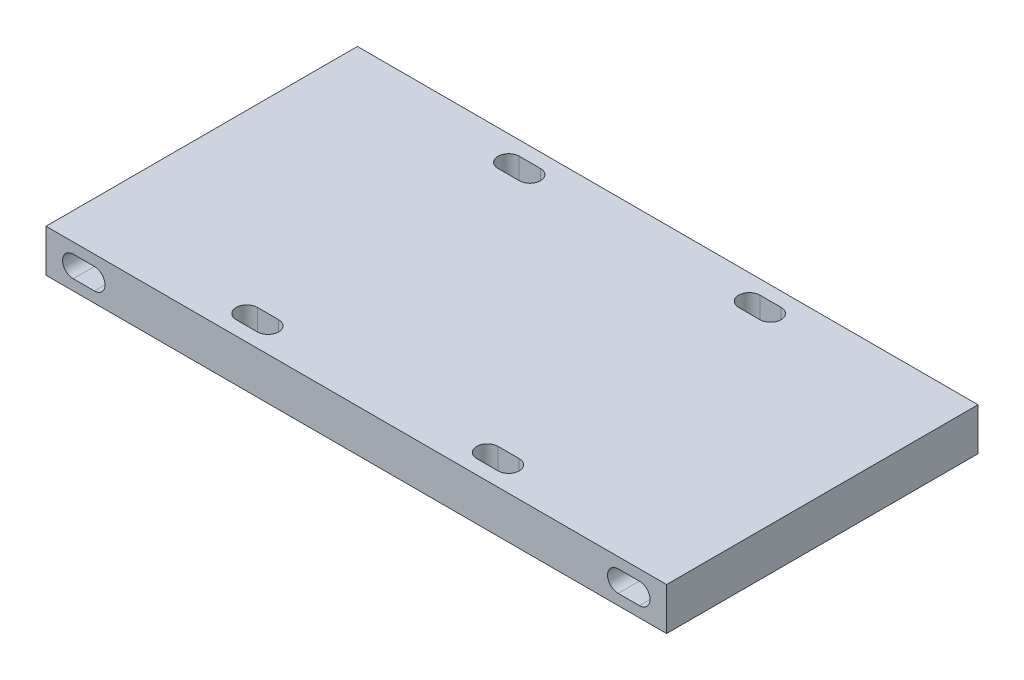
SolidWorks part; units mm, degrees
ref_plane "前视基准面" through (0, 0, 0) normal (0, 0, 1) x (1, 0, 0)
ref_plane "上视基准面" through (0, 0, 0) normal (0, 1, 0) x (1, 0, 0)
ref_plane "右视基准面" through (0, 0, 0) normal (1, 0, 0) x (0, 0, -1)
sketch "草图1" plane through (0, 0, 0) normal (0, 0, 1) x (1, 0, 0)
  line L0 (-40, 0) -> (40, 0) construction
  line L1 (-43.8406, 3) -> (43.8406, 3)
  line L2 (-43.8406, 3) -> (-43.8406, -3)
  line L3 (-43.8406, -3) -> (43.8406, -3)
  line L4 (43.8406, 3) -> (43.8406, -3)
  line L5 (-43.8406, 3) -> (43.8406, -3) construction
  line L6 (-43.8406, -3) -> (43.8406, 3) construction
  line L7 (-40, 0) -> (-37, 0) construction
  line L8 (-40, 1.5) -> (-37, 1.5)
  line L9 (-40, -1.5) -> (-37, -1.5)
  line L10 (0, 0) -> (0, 3) construction
  line L11 (40, 0) -> (37, 0) construction
  line L12 (40, 1.5) -> (37, 1.5)
  line L13 (40, -1.5) -> (37, -1.5)
  arc A0 (-40, 1.5) -> (-40, -1.5) centre (-40, 0) ccw
  arc A1 (-37, -1.5) -> (-37, 1.5) centre (-37, 0) ccw
  arc A2 (40, 1.5) -> (40, -1.5) centre (40, 0) cw
  arc A3 (37, -1.5) -> (37, 1.5) centre (37, 0) cw
  point P0 (0, 0)
  point P6 (-38.5, 0)
  point P9 (0, 0)
  point P18 (38.5, 0)
  dimension "D4" = 1.5
  dimension "D1" = 87.6812
  dimension "D2" = 6
  dimension "D3" = 3
extrude "凸台-拉伸1" add sketch "草图1" along normal blind 44
sketch "草图2" plane through (0, -3, 0) normal (0, -1, 0) x (-1, 0, 0)
  line L0 (2.1436, -22.9628) -> (9.3627, -10.4589)
  line L1 (9.3627, -10.4589) -> (4.6305, -10.4589)
  line L2 (4.6305, -10.4589) -> (-1.7817, -21.5652)
  line L3 (-1.7817, -21.5652) -> (0.0481, -26.5924)
  line L4 (0.0481, -26.5924) -> (-2.5682, -31.1239)
  line L5 (-2.5682, -31.1239) -> (-8.5375, -14.7234)
  line L6 (-8.5375, -14.7234) -> (-1.867, -14.7234)
  line L7 (-1.867, -14.7234) -> (-3.4191, -10.4589)
  line L8 (-3.4191, -10.4589) -> (-14.5058, -10.4589)
  line L9 (-14.5058, -10.4589) -> (-6.9844, -31.1239)
  point P9 (0, 0)
  dimension "D1" = 70
  dimension "D2" = 60
extrude "切除-拉伸-薄壁1" cut sketch "草图2" against normal blind 1 and the other way through all thin thin type mid plane wall 2
sketch "草图3" plane through (0, -3, 0) normal (0, -1, 0) x (1, 0, 0)
  line L0 (-18.9761, 40.5) -> (-15.9761, 40.5) construction
  line L1 (-18.9761, 40.5) -> (18.0239, 40.5)
  line L2 (-18.9761, 40.5) -> (-18.9761, 3.5)
  line L3 (-18.9761, 3.5) -> (18.0239, 3.5)
  line L4 (18.0239, 40.5) -> (18.0239, 3.5)
  line L5 (-18.9761, 40.5) -> (18.0239, 3.5) construction
  line L6 (-18.9761, 3.5) -> (18.0239, 40.5) construction
  line L7 (-18.9761, 42) -> (-15.9761, 42)
  line L8 (-18.9761, 39) -> (-15.9761, 39)
  line L9 (-0.4761, 43.5) -> (-0.4761, -0.5) construction
  line L11 (43.8406, 22) -> (-44.0685, 22) construction
  line L13 (18.0239, 40.5) -> (15.0239, 40.5) construction
  line L14 (18.0239, 42) -> (15.0239, 42)
  line L15 (18.0239, 39) -> (15.0239, 39)
  line L16 (18.0239, 3.5) -> (15.0239, 3.5) construction
  line L17 (18.0239, 2) -> (15.0239, 2)
  line L18 (18.0239, 5) -> (15.0239, 5)
  line L19 (-18.9761, 3.5) -> (-15.9761, 3.5) construction
  line L20 (-18.9761, 2) -> (-15.9761, 2)
  line L21 (-18.9761, 5) -> (-15.9761, 5)
  arc A0 (-18.9761, 42) -> (-18.9761, 39) centre (-18.9761, 40.5) ccw
  arc A1 (-15.9761, 39) -> (-15.9761, 42) centre (-15.9761, 40.5) ccw
  arc A2 (18.0239, 42) -> (18.0239, 39) centre (18.0239, 40.5) cw
  arc A3 (15.0239, 39) -> (15.0239, 42) centre (15.0239, 40.5) cw
  arc A4 (18.0239, 2) -> (18.0239, 5) centre (18.0239, 3.5) ccw
  arc A5 (15.0239, 5) -> (15.0239, 2) centre (15.0239, 3.5) ccw
  arc A6 (-18.9761, 2) -> (-18.9761, 5) centre (-18.9761, 3.5) cw
  arc A7 (-15.9761, 5) -> (-15.9761, 2) centre (-15.9761, 3.5) cw
  point P0 (-0.4761, 22)
  point P5 (-17.4761, 40.5)
  point P13 (0, 21.8366)
  point P14 (-0.4761, 22)
  point P19 (16.5239, 40.5)
  point P25 (16.5239, 3.5)
  point P31 (-17.4761, 3.5)
  dimension "D4" = 1.5
  dimension "D1" = 37
  dimension "D2" = 37
  dimension "D3" = 3
extrude "切除-拉伸1" cut sketch "草图3" against normal blind 44 contours L1 A1 L7 A0 L2 | A3 L1 L4 A2 L14 | L3 A5 L17 A4 L4 | A7 L3 L2 A6 L20 | A7 L21 L2 L3 | L8 A1 L1 L2 | A3 L15 L4 L1 | L18 A5 L3 L4
